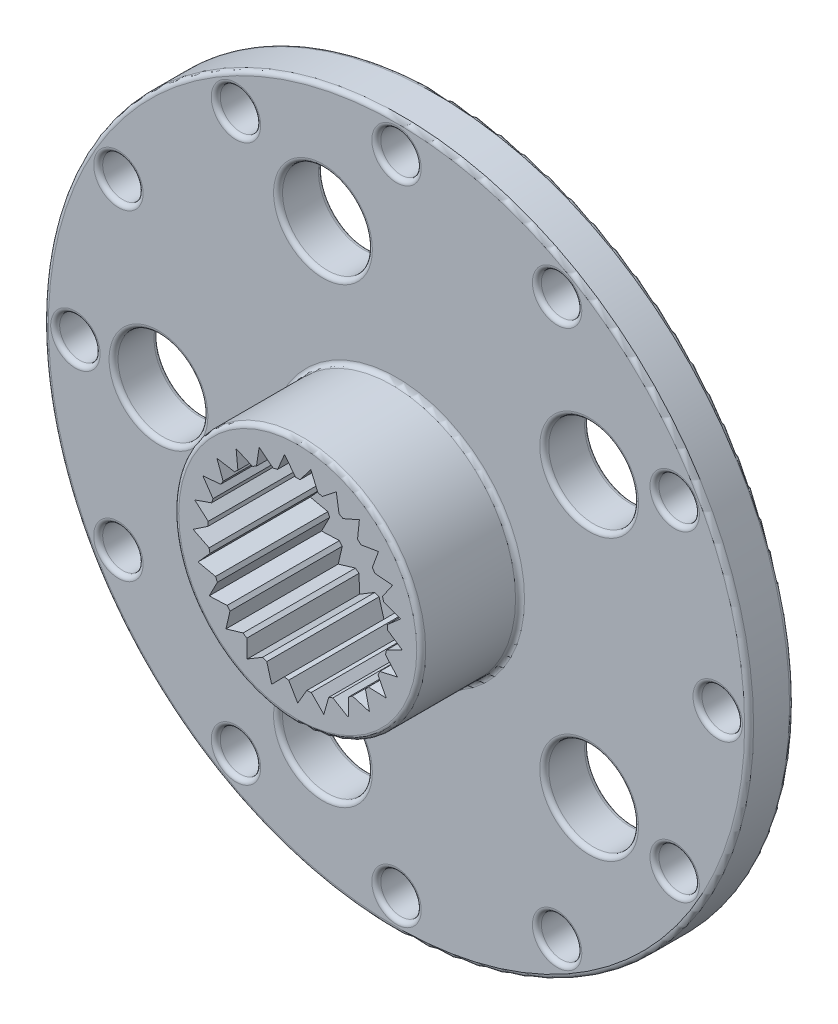
SolidWorks part; units mm, degrees
material "ABS"
ref_plane "Plan de face" through (0, 0, 0) normal (0, 0, 1) x (1, 0, 0)
ref_plane "Plan de dessus" through (0, 0, 0) normal (0, 1, 0) x (1, 0, 0)
ref_plane "Plan de droite" through (0, 0, 0) normal (1, 0, 0) x (0, 0, -1)
sketch "Esquisse1" plane through (0, 0, 0) normal (0, 0, 1) x (1, 0, 0)
  line L0 (-25.8199, 1.564) -> (18.3852, 1.564) construction
  line L5 (0, 0) -> (0, -2.75) construction
  circle A0 centre (0, 0) radius 2.75
  circle A1 centre (0, 0) radius 7.85
  dimension "D1" = 5.5
  dimension "D2" = 15.7
extrude "Boss.-Extru.1" add sketch "Esquisse1" along normal blind 1
sketch "Esquisse2" plane through (0, 0, 1) normal (0, 0, 1) x (1, 0, 0)
  circle A0 centre (0, 0) radius 2.75
  dimension "D1" = 5.5
extrude "Boss.-Extru.2" add sketch "Esquisse2" along normal offset from surface (2.2 mm away) 3.2 up to face at (7.85, 0, 0)
sketch "Esquisse3" plane through (0, 0, 3.2) normal (0, 0, 1) x (1, 0, 0)
  circle A0 centre (0, 0) radius 2
  dimension "D1" = 4
extrude "Enlèv. mat.-Extru.1" cut sketch "Esquisse3" against normal blind 2.5
sketch "Sketch1" plane through (0, 0, 3.2) normal (0, 0, 1) x (1, 0, 0)
  line L0 (0, 0) -> (0, -2) construction
  line L1 (0, 0) -> (0.2007, -1.9899) construction
  line L2 (0, 0) -> (-0.2007, -1.9899) construction
  line L3 (0.2007, -1.9899) -> (0, -2.334)
  line L4 (0, -2.334) -> (-0.2007, -1.9899)
  circle A0 centre (0, 0) radius 2 construction
  circle A1 centre (0, 0) radius 2 construction
  arc A2 (-0.2007, -1.9899) -> (0.2007, -1.9899) centre (0, 0) ccw
  circle A3 centre (0, 0) radius 2.334 construction
  dimension "D3" = 4.668
  dimension "D1" = 5.76
  dimension "D2" = 5.76
extrude "Cut-Extrude1" cut sketch "Sketch1" against normal up to surface (2.5 mm away) contours L4 A2 L3 up to face at (2, 0, 0.7)
pattern_circular "CirPattern1" count 25 over 360 about axis through (0, 0, 0) along (0, 0, 1) of "Cut-Extrude1"
sketch "Esquisse4" plane through (0, 0, 0) normal (0, 0, -1) x (-1, 0, 0)
  circle A0 centre (0, 0) radius 1.6
  dimension "D1" = 3.2
extrude "Enlèv. mat.-Extru.2" cut sketch "Esquisse4" against normal blind 0.4
sketch "Esquisse5" plane through (0, 0, 0.4) normal (0, 0, -1) x (-1, 0, 0)
  circle A0 centre (0, 0) radius 0.85
  dimension "D1" = 1.7
extrude "Enlèv. mat.-Extru.3" cut sketch "Esquisse5" against normal blind 4.8
hole_wizard "Ø0.9 (0.9) Diameter Hole1" positions "Sketch3" profile "Sketch2" hole size "Ø0.9" standard "ANSI Metric" end condition through all
sketch "Sketch3" plane through (0, 0, 0) normal (0, 0, -1) x (-1, 0, 0)
  line L2 (7.15, 0) -> (-7.15, 0) construction
  point P21 (7.15, 0)
  dimension "D1" = 14.3
sketch "Sketch2" plane through (-7.15, 0, 0) normal (1, 0, 0) x (0, 1, 0)
  line L0 (0, 0) -> (0, 3.2)
  line L1 (0, 3.2) -> (0.45, 3.2)
  line L2 (0.45, 3.2) -> (0.45, 0)
  line L5 (0.45, 0) -> (0, 0)
  line L11 (0, -6.35) -> (0, 107.95) construction
  dimension "Thru Hole Dia." = 0.9
  dimension "Thru Hole Depth" = 3.2
pattern_circular "CirPattern2" count 12 over 360 about axis through (0, 0, 0) along (0, 0, 1) of "Ø0.9 (0.9) Diameter Hole1"
hole_wizard "Ø2.0 (2) Diameter Hole1" positions "Sketch5" profile "Sketch4" hole size "Ø2.0" standard "ANSI Metric" end condition through all
sketch "Sketch5" plane through (0, 0, 0) normal (0, 0, -1) x (-1, 0, 0)
  line L0 (5.3, 0) -> (-5.3, 0) construction
  point P0 (5.3, 0)
  dimension "D1" = 10.6
sketch "Sketch4" plane through (-5.3, 0, 0) normal (1, 0, 0) x (0, 1, 0)
  line L0 (0, 0) -> (0, 3.2)
  line L1 (0, 3.2) -> (1, 3.2)
  line L2 (1, 3.2) -> (1, 0)
  line L5 (1, 0) -> (0, 0)
  line L11 (0, -6.35) -> (0, 107.95) construction
  dimension "Thru Hole Dia." = 2
  dimension "Thru Hole Depth" = 3.2
pattern_circular "CirPattern3" count 5 over 360 about axis through (0, 0, 0) along (0, 0, 1) of "Ø2.0 (2) Diameter Hole1"
fillet "Fillet1" radius 0.1 39 edges at (7.85, 0, 1) (2.75, 0, 1) (-6.7, 0, 1) (-5.7421, 3.575, 1) (-3.125, 6.1921, 1) (0.45, 7.15, 1) (4.025, 6.1921, 1) (6.6421, 3.575, 1) (7.6, 0, 1) (6.6421, -3.575, 1) (4.025, -6.1921, 1) (0.45, -7.15, 1) (-3.125, -6.1921, 1) (-5.7421, -3.575, 1) (-4.3, 0, 1) (-0.6378, 5.0406, 1) (5.2878, 3.1153, 1) (5.2878, -3.1153, 1) (-0.6378, -5.0406, 1) (-0.45, 7.15, 0) (7.85, 0, 0) (-1.6, 0, 0) (-7.6, 0, 0) (-6.6421, 3.575, 0) (-4.025, 6.1921, 0) (3.125, 6.1921, 0) (5.7421, 3.575, 0) (6.7, 0, 0) (5.7421, -3.575, 0) (3.125, -6.1921, 0) (-0.45, -7.15, 0) (-4.025, -6.1921, 0) (-6.6421, -3.575, 0) (-6.3, 0, 0) (-2.6378, 5.0406, 0) (3.2878, 3.1153, 0) (3.2878, -3.1153, 0) (-2.6378, -5.0406, 0) (2.75, 0, 3.2)
equation "\"D2@Sketch1\"=\"D1@Sketch1\""
